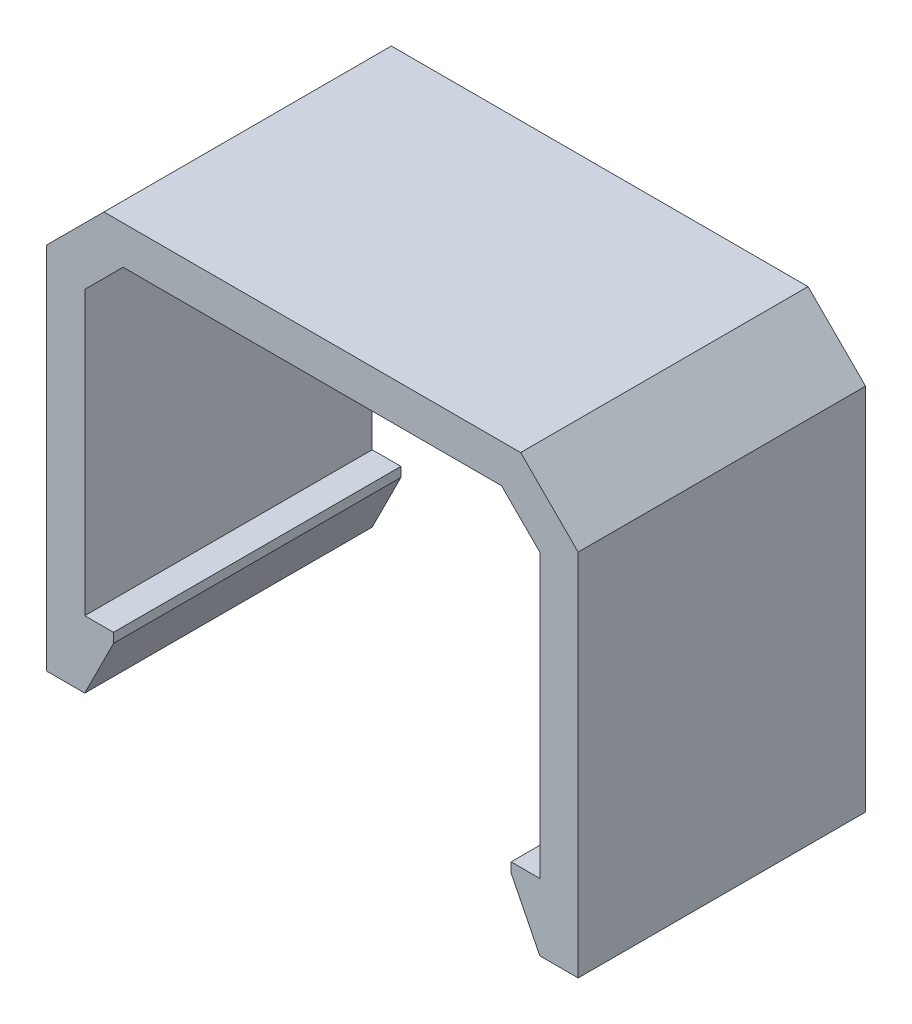
SolidWorks part; units mm, degrees
ref_plane "Front Plane" through (0, 0, 0) normal (0, 0, 1) x (1, 0, 0)
ref_plane "Top Plane" through (0, 0, 0) normal (0, 1, 0) x (1, 0, 0)
ref_plane "Right Plane" through (0, 0, 0) normal (1, 0, 0) x (0, 0, -1)
sketch "Sketch1" plane through (0, 0, 0) normal (0, 0, 1) x (1, 0, 0)
  line L0 (0, 0) -> (0, 16.75)
  line L1 (0, 16.75) -> (23.75, 16.75)
  line L2 (23.75, 16.75) -> (23.75, 0)
  line L3 (0, 0) -> (1.5, 0)
  line L4 (1.5, 0) -> (1.5, -3.5)
  line L5 (1.5, -3.5) -> (-2, -3.5)
  line L6 (11.875, 16.75) -> (11.875, 18.75)
  line L7 (25.75, 18.75) -> (-2, 18.75)
  line L8 (-2, 18.75) -> (-2, -3.5)
  line L9 (25.75, 18.75) -> (25.75, -3.5)
  line L10 (22.25, -3.5) -> (25.75, -3.5)
  line L11 (22.25, 0) -> (22.25, -3.5)
  line L12 (23.75, 0) -> (22.25, 0)
  line L13 (23.75, 0) -> (23.75, 16.75)
  dimension "D1" = 2
  dimension "D2" = 2
  dimension "D3" = 23.75
  dimension "D4" = 16.75
extrude "Boss-Extrude1" add sketch "Sketch1" along normal blind 15 contours L7 L8 L5 L4 L3 L0 L1 L6 | L2 L12 L11 L10 L9 L7 L6 L1
chamfer "Chamfer1" distance 3 angle 45 2 edges at (25.75, 18.75, 7.5) (-2, 18.75, 7.5)
chamfer "Chamfer2" distance 2 angle 45 2 edges at (23.75, 16.75, 7.5) (0, 16.75, 7.5)
chamfer "Chamfer3" distance 1.5 distance2 3 1 edges at (1.5, -3.5, 7.5)
chamfer "Chamfer4" distance 3 distance2 1.5 1 edges at (22.25, -3.5, 7.5)
